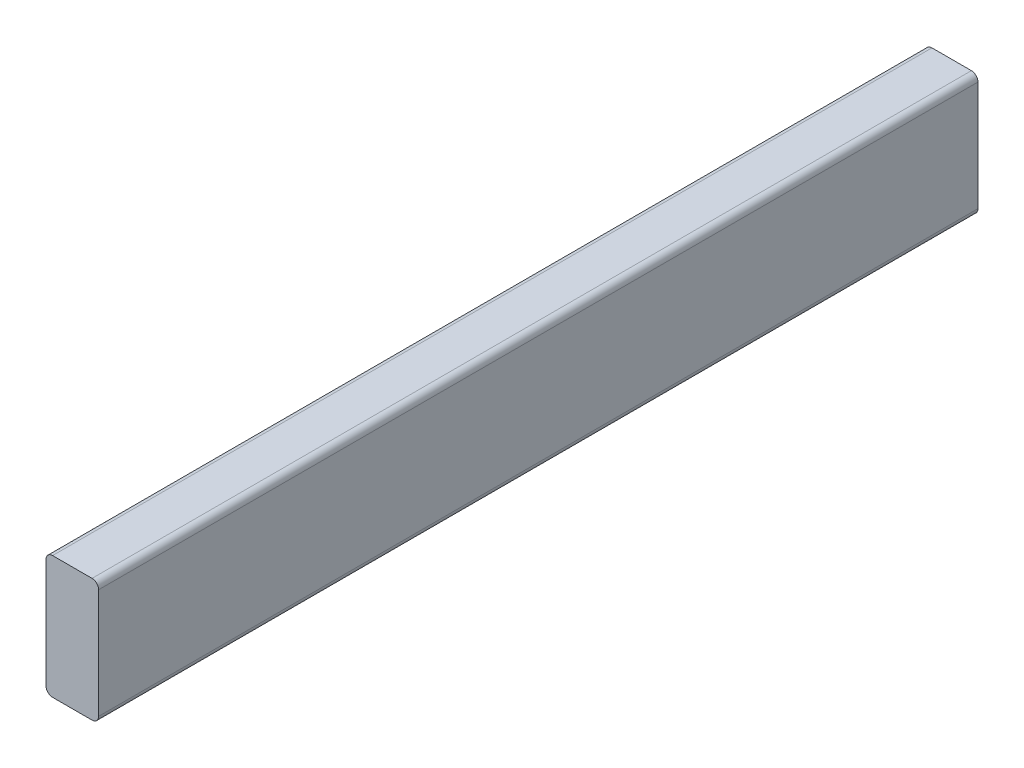
SolidWorks part; units mm, degrees
material "Pine"
ref_plane "Front Plane" through (0, 0, 0) normal (0, 0, 1) x (1, 0, 0)
ref_plane "Top Plane" through (0, 0, 0) normal (0, 1, 0) x (1, 0, 0)
ref_plane "Right Plane" through (0, 0, 0) normal (1, 0, 0) x (0, 0, -1)
sketch "Sketch1" plane through (0, 0, 0) normal (0, 0, 1) x (1, 0, 0)
  line L1 (-819.8306, 100.8062) -> (-781.7306, 100.8062)
  line L2 (-819.8306, 100.8062) -> (-819.8306, 11.9062)
  line L3 (-819.8306, 11.9062) -> (-781.7306, 11.9062)
  line L4 (-781.7306, 100.8062) -> (-781.7306, 11.9062)
extrude "Boss-Extrude1" add sketch "Sketch1" against normal up to surface (636.6692 mm away)
fillet "Fillet1" radius 4.7625 4 edges at (-819.8306, 11.9062, -318.3346) (-781.7306, 11.9062, -318.3346) (-819.8306, 100.8062, -318.3346) (-781.7306, 100.8062, -318.3346)
